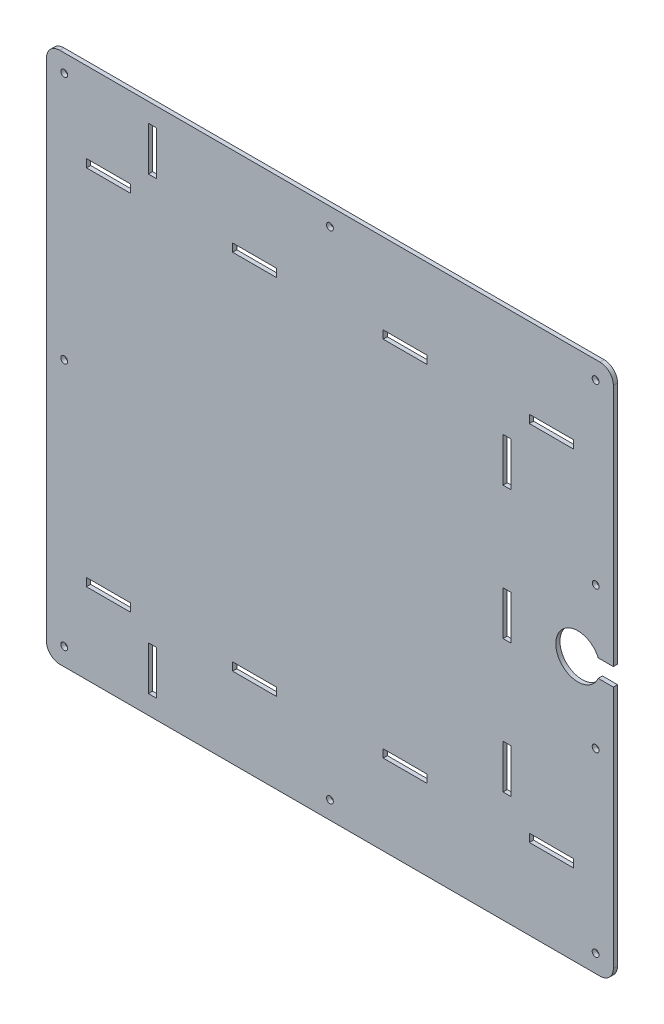
SolidWorks part; units mm, degrees
material "Balsa"
ref_plane "Front Plane" through (0, 0, 0) normal (0, 0, 1) x (1, 0, 0)
ref_plane "Top Plane" through (0, 0, 0) normal (0, 1, 0) x (1, 0, 0)
ref_plane "Right Plane" through (0, 0, 0) normal (1, 0, 0) x (0, 0, -1)
sketch "Sketch1" plane through (0, 0, 0) normal (0, 0, 1) x (1, 0, 0)
  line L0 (-135.8663, -66.675) -> (-135.8663, -314.579)
  line L39 (270.5337, -82.55) -> (270.5337, -9.525)
  line L40 (261.0087, 0) -> (-126.3413, 0)
  line L41 (-135.8663, -9.525) -> (-135.8663, -66.675)
  line L49 (259.6834, -184.277) -> (270.5337, -184.277)
  line L50 (270.5337, -184.277) -> (270.5337, -82.55)
  line L66 (270.5337, -298.704) -> (270.5337, -196.977)
  line L67 (270.5337, -196.977) -> (259.6834, -196.977)
  line L68 (270.5337, -371.729) -> (270.5337, -298.704)
  line L76 (-135.8663, -314.579) -> (-135.8663, -371.729)
  line L77 (-126.3413, -381.254) -> (261.0087, -381.254)
  arc A7 (270.5337, -9.525) -> (261.0087, 0) centre (261.0087, -9.525) ccw
  arc A8 (-126.3413, 0) -> (-135.8663, -9.525) centre (-126.3413, -9.525) ccw
  arc A10 (259.6834, -184.277) -> (259.6834, -196.977) centre (245.1337, -190.627) ccw
  arc A12 (-135.8663, -371.729) -> (-126.3413, -381.254) centre (-126.3413, -371.729) ccw
  arc A13 (261.0087, -381.254) -> (270.5337, -371.729) centre (261.0087, -371.729) ccw
  dimension "D4" = 15.875
  dimension "D5" = 9.525
  dimension "D1" = 406.4
  dimension "D2" = 381.254
  dimension "D3" = 25.4
  dimension "D6" = 245.1337
  dimension "D7" = 259.6834
  dimension "D8" = 66.675
  dimension "D9" = 82.55
  dimension "D10" = 12.7
extrude "Boss-Extrude1" add sketch "Sketch1" along normal blind 3
hole_wizard "#10 (0.1935) Diameter Hole3" positions "3DSketch1" profile "Sketch2" hole size "#10" standard "ANSI Inch"
sketch3d "3DSketch1"
  line L0 (261.0087, 0, 3) -> (-126.3413, 0, 3) construction
  line L1 (-135.8663, -9.525, 3) -> (-135.8663, -371.729, 3) construction
  point P0 (-123.1663, -12.7, 3)
  dimension "D1" = 12.7
  dimension "D2" = 12.7
sketch "Sketch2" plane through (-123.1663, -12.7, 3) normal (1, 0, 0) x (0, -1, 0)
  line L0 (0, 0) -> (0, 77.6766)
  line L1 (0, 77.6766) -> (2.4574, 76.2)
  line L2 (2.4574, 76.2) -> (2.4574, 0)
  line L5 (2.4574, 0) -> (0, 0)
  line L10 (0, 77.6766) -> (-2.4575, 76.2) construction
  line L11 (0, -6.35) -> (0, 107.95) construction
  dimension "Hole Dia." = 4.9149
  dimension "Hole Depth" = 76.2
  dimension "Drill Angle" = 118
ref_plane "Plane2" through (67.3337, 0, 0) normal (-1, 0, 0) x (0, 0, 1)
ref_plane "Plane3" through (0, -190.627, 0) normal (0, 1, 0) x (1, 0, 0)
hole_wizard "#10 (0.1935) Diameter Hole2" positions "3DSketch3" profile "Sketch7" hole size "#10" standard "ANSI Inch"
sketch3d "3DSketch3"
  line L0 (261.0087, 0, 0) -> (-126.3413, 0, 0) construction
  line L1 (67.3337, -381.254, 0) -> (67.3337, 0, 0) construction
  line L2 (-126.3413, -381.254, 0) -> (261.0087, -381.254, 0) construction
  line L4 (-135.8663, -190.627, 0) -> (306.0951, -190.627, 0) construction
  line L5 (-135.8663, -9.525, 0) -> (-135.8663, -371.729, 0) construction
  point P0 (67.3337, -12.7, 0)
  point P16 (-123.1663, -190.627, 0)
  dimension "D1" = 12.7
  dimension "D2" = 12.7
sketch "Sketch7" plane through (67.3337, -12.7, 0) normal (1, 0, 0) x (0, 1, 0)
  line L0 (0, 0) -> (0, 77.6766)
  line L1 (0, 77.6766) -> (2.4574, 76.2)
  line L2 (2.4574, 76.2) -> (2.4574, 0)
  line L5 (2.4574, 0) -> (0, 0)
  line L10 (0, 77.6766) -> (-2.4575, 76.2) construction
  line L11 (0, -6.35) -> (0, 107.95) construction
  dimension "Hole Dia." = 4.9149
  dimension "Hole Depth" = 76.2
  dimension "Drill Angle" = 118
mirror "Mirror1" about plane through (67.3337, 0, 0) normal (-1, 0, 0) of "#10 (0.1935) Diameter Hole3"
mirror "Mirror2" about plane through (0, -190.627, 0) normal (0, 1, 0) of "Mirror1", "#10 (0.1935) Diameter Hole3", "#10 (0.1935) Diameter Hole2"
hole_wizard "#10 (0.1935) Diameter Hole1" positions "3DSketch4" profile "Sketch8" hole size "#10" standard "ANSI Inch"
sketch3d "3DSketch4"
  line L0 (257.8337, -241.427, 0) -> (257.901, -139.827, 0) construction
  line L2 (-135.8663, -190.627, 0) -> (369.2975, -190.627, 0) construction
  line L3 (-135.8663, -9.525, 0) -> (-135.8663, -371.729, 0) construction
  line L5 (270.5337, -371.729, 0) -> (270.5337, -196.977, 0) construction
  point P0 (257.8337, -241.427, 0)
  point P2 (257.901, -139.827, 0)
  point P13 (257.8674, -190.627, 0)
  dimension "D1" = 12.7
  dimension "D2" = 101.6
sketch "Sketch8" plane through (257.8337, -241.427, 0) normal (1, 0, 0) x (0, 1, 0)
  line L0 (0, 0) -> (0, 77.6766)
  line L1 (0, 77.6766) -> (2.4574, 76.2)
  line L2 (2.4574, 76.2) -> (2.4574, 0)
  line L5 (2.4574, 0) -> (0, 0)
  line L10 (0, 77.6766) -> (-2.4575, 76.2) construction
  line L11 (0, -6.35) -> (0, 107.95) construction
  dimension "Hole Dia." = 4.9149
  dimension "Hole Depth" = 76.2
  dimension "Drill Angle" = 118
sketch "Sketch9" plane through (0, 0, 0) normal (0, 0, -1) x (-1, 0, 0)
  line L0 (-270.5337, -371.729) -> (-270.5337, -196.977) construction
  line L1 (-210.3103, -323.5579) -> (-241.8571, -323.5579)
  line L2 (-210.3103, -323.5579) -> (-210.3103, -317.7921)
  line L3 (-210.3103, -317.7921) -> (-241.8571, -317.7921)
  line L4 (-241.8571, -323.5579) -> (-241.8571, -317.7921)
  line L5 (-210.3103, -323.5579) -> (-241.8571, -317.7921) construction
  line L6 (-210.3103, -317.7921) -> (-241.8571, -323.5579) construction
  line L7 (-105.5353, -63.4619) -> (-137.0821, -57.6961) construction
  line L8 (-67.3337, -381.254) -> (-67.3337, 0) construction
  line L9 (126.3413, -381.254) -> (-261.0087, -381.254) construction
  line L10 (-261.0087, 0) -> (126.3413, 0) construction
  line L11 (135.8663, -190.627) -> (-400.4137, -190.627) construction
  line L12 (135.8663, -9.525) -> (135.8663, -371.729) construction
  line L13 (75.6429, -323.5579) -> (75.6429, -317.7921)
  line L14 (75.6429, -317.7921) -> (107.1897, -317.7921)
  line L15 (107.1897, -323.5579) -> (107.1897, -317.7921)
  line L16 (75.6429, -323.5579) -> (107.1897, -323.5579)
  line L19 (-241.8571, -57.6961) -> (-241.8571, -63.4619)
  line L25 (-191.4508, -79.6036) -> (-197.2166, -79.6036)
  line L26 (-191.4508, -301.6504) -> (-197.2166, -301.6504)
  line L27 (-191.4508, -301.6504) -> (-191.4508, -270.1036)
  line L28 (-191.4508, -270.1036) -> (-197.2166, -270.1036)
  line L29 (-197.2166, -301.6504) -> (-197.2166, -270.1036)
  line L30 (-191.4508, -301.6504) -> (-197.2166, -270.1036) construction
  line L31 (-191.4508, -270.1036) -> (-197.2166, -301.6504) construction
  line L32 (-197.2166, -79.6036) -> (-197.2166, -111.1504)
  line L33 (-191.4508, -111.1504) -> (-197.2166, -111.1504)
  line L34 (-191.4508, -79.6036) -> (-191.4508, -111.1504)
  line L35 (-29.1321, -323.5579) -> (-29.1321, -317.7921)
  line L36 (-197.2166, -206.4004) -> (-191.4508, -206.4004)
  line L37 (-197.2166, -206.4004) -> (-197.2166, -174.8536)
  line L38 (-197.2166, -174.8536) -> (-191.4508, -174.8536)
  line L39 (-191.4508, -206.4004) -> (-191.4508, -174.8536)
  line L40 (-197.2166, -206.4004) -> (-191.4508, -174.8536) construction
  line L41 (-197.2166, -174.8536) -> (-191.4508, -206.4004) construction
  line L42 (-105.5353, -323.5579) -> (-137.0821, -323.5579)
  line L43 (-105.5353, -323.5579) -> (-105.5353, -317.7921)
  line L44 (-105.5353, -317.7921) -> (-137.0821, -317.7921)
  line L45 (-137.0821, -323.5579) -> (-137.0821, -317.7921)
  line L46 (-105.5353, -323.5579) -> (-137.0821, -317.7921) construction
  line L47 (-105.5353, -317.7921) -> (-137.0821, -323.5579) construction
  line L48 (-29.1321, -317.7921) -> (2.4147, -317.7921)
  line L49 (2.4147, -323.5579) -> (2.4147, -317.7921)
  line L50 (-29.1321, -323.5579) -> (2.4147, -323.5579)
  line L51 (-105.5353, -57.6961) -> (-137.0821, -63.4619) construction
  line L52 (-210.3103, -63.4619) -> (-241.8571, -57.6961) construction
  line L53 (-210.3103, -57.6961) -> (-241.8571, -63.4619) construction
  line L54 (-29.1321, -57.6961) -> (2.4147, -57.6961)
  line L55 (2.4147, -57.6961) -> (2.4147, -63.4619)
  line L56 (-29.1321, -63.4619) -> (2.4147, -63.4619)
  line L57 (-137.0821, -57.6961) -> (-137.0821, -63.4619)
  line L58 (-105.5353, -63.4619) -> (-137.0821, -63.4619)
  line L59 (-105.5353, -57.6961) -> (-105.5353, -63.4619)
  line L60 (-105.5353, -57.6961) -> (-137.0821, -57.6961)
  line L61 (-29.1321, -57.6961) -> (-29.1321, -63.4619)
  line L62 (75.6429, -57.6961) -> (107.1897, -57.6961)
  line L63 (107.1897, -57.6961) -> (107.1897, -63.4619)
  line L64 (75.6429, -63.4619) -> (107.1897, -63.4619)
  line L65 (75.6429, -57.6961) -> (75.6429, -63.4619)
  line L66 (-241.8571, -57.6961) -> (-241.8571, -63.4619)
  line L67 (-210.3103, -63.4619) -> (-241.8571, -63.4619)
  line L68 (-210.3103, -57.6961) -> (-210.3103, -63.4619)
  line L69 (-210.3103, -57.6961) -> (-241.8571, -57.6961)
  line L70 (57.0501, -13.5712) -> (62.8159, -13.5712)
  line L71 (57.0501, -367.6828) -> (62.8159, -367.6828)
  line L72 (57.0501, -367.6828) -> (57.0501, -336.136)
  line L73 (57.0501, -336.136) -> (62.8159, -336.136)
  line L74 (62.8159, -367.6828) -> (62.8159, -336.136)
  line L75 (57.0501, -367.6828) -> (62.8159, -336.136) construction
  line L76 (57.0501, -336.136) -> (62.8159, -367.6828) construction
  line L77 (62.8159, -13.5712) -> (62.8159, -45.118)
  line L78 (57.0501, -45.118) -> (62.8159, -45.118)
  line L79 (57.0501, -13.5712) -> (57.0501, -45.118)
  line L80 (135.8663, -9.525) -> (135.8663, -371.729) construction
  point P0 (-226.0837, -320.675)
  point P25 (-241.8571, -60.579)
  point P30 (-194.3337, -285.877)
  point P39 (-194.3337, -190.627)
  point P44 (-121.3087, -320.675)
  point P53 (-13.3587, -323.5579)
  point P62 (-121.3087, -60.579)
  point P63 (-226.0837, -60.579)
  point P64 (59.933, -351.9094)
  dimension "D1" = 44.45
  dimension "D2" = 31.5468
  dimension "D3" = 5.7658
  dimension "D4" = 260.096
  dimension "D5" = 76.2
  dimension "D6" = 95.25
  dimension "D7" = 107.95
  dimension "D8" = 73.0504
  dimension "D9" = 28.3515
extrude "Cut-Extrude1" cut sketch "Sketch9" against normal through all contours L45 L42 L43 L44 | L4 L1 L2 L3 | L29 L26 L27 L28 | L36 L39 L38 L37 | L34 L25 L32 L33 | L68 L69 L19 L67 | L59 L60 L57 L58 | L54 L61 L56 L55 | L62 L65 L64 L63 | L71 L74 L73 L72 | L70 L79 L78 L77 | L14 L15 L16 L13 | L48 L49 L50 L35
sketch "Sketch10" plane through (0, 0, 3) normal (0, 0, 1) x (1, 0, 0)
  line L0 (-62.7143, -13.6728) -> (-62.7143, -45.0164)
  line L1 (-62.7143, -45.0164) -> (-57.1517, -45.0164)
  line L2 (-57.1517, -45.0164) -> (-57.1517, -13.6728)
  line L3 (-57.1517, -13.6728) -> (-62.7143, -13.6728)
  line L4 (-62.8159, -13.5712) -> (-62.8159, -45.118)
  line L5 (-57.0501, -13.5712) -> (-62.8159, -13.5712)
  line L6 (-57.0501, -45.118) -> (-57.0501, -13.5712)
  line L7 (270.5337, -184.277) -> (270.5337, -9.525)
  line L8 (261.0087, 0) -> (-126.3413, 0)
  line L9 (-135.8663, -9.525) -> (-135.8663, -371.729)
  line L10 (-126.3413, -381.254) -> (261.0087, -381.254)
  line L11 (270.5337, -371.729) -> (270.5337, -196.977)
  line L12 (270.5337, -196.977) -> (259.6834, -196.977)
  line L13 (259.6834, -184.277) -> (270.5337, -184.277)
  line L14 (270.5337, -184.277) -> (270.5337, -9.525) construction
  line L15 (261.0087, 0) -> (-126.3413, 0) construction
  line L16 (-135.8663, -9.525) -> (-135.8663, -371.729) construction
  line L17 (-126.3413, -381.254) -> (261.0087, -381.254) construction
  line L18 (270.5337, -371.729) -> (270.5337, -196.977) construction
  line L19 (270.5337, -196.977) -> (259.6834, -196.977) construction
  line L20 (259.6834, -184.277) -> (270.5337, -184.277) construction
  line L21 (-62.8159, -45.118) -> (-57.0501, -45.118)
  line L22 (-62.8159, -13.5712) -> (-62.8159, -45.118) construction
  line L23 (-57.0501, -13.5712) -> (-62.8159, -13.5712) construction
  line L24 (-57.0501, -45.118) -> (-57.0501, -13.5712) construction
  line L25 (-62.8159, -45.118) -> (-57.0501, -45.118) construction
  line L26 (-107.1897, -57.6961) -> (-107.1897, -63.4619)
  line L27 (-75.6429, -57.6961) -> (-107.1897, -57.6961)
  line L28 (-75.6429, -63.4619) -> (-75.6429, -57.6961)
  line L29 (-107.1897, -63.4619) -> (-75.6429, -63.4619)
  line L30 (-107.1897, -57.6961) -> (-107.1897, -63.4619) construction
  line L31 (-75.6429, -57.6961) -> (-107.1897, -57.6961) construction
  line L32 (-75.6429, -63.4619) -> (-75.6429, -57.6961) construction
  line L33 (-107.1897, -63.4619) -> (-75.6429, -63.4619) construction
  line L34 (-2.4147, -57.6961) -> (-2.4147, -63.4619)
  line L35 (29.1321, -57.6961) -> (-2.4147, -57.6961)
  line L36 (29.1321, -63.4619) -> (29.1321, -57.6961)
  line L37 (-2.4147, -63.4619) -> (29.1321, -63.4619)
  line L38 (-2.4147, -57.6961) -> (-2.4147, -63.4619) construction
  line L39 (29.1321, -57.6961) -> (-2.4147, -57.6961) construction
  line L40 (29.1321, -63.4619) -> (29.1321, -57.6961) construction
  line L41 (-2.4147, -63.4619) -> (29.1321, -63.4619) construction
  line L42 (105.5353, -63.4619) -> (137.0821, -63.4619)
  line L43 (105.5353, -57.6961) -> (105.5353, -63.4619)
  line L44 (137.0821, -57.6961) -> (105.5353, -57.6961)
  line L45 (137.0821, -63.4619) -> (137.0821, -57.6961)
  line L46 (105.5353, -63.4619) -> (137.0821, -63.4619) construction
  line L47 (105.5353, -57.6961) -> (105.5353, -63.4619) construction
  line L48 (137.0821, -57.6961) -> (105.5353, -57.6961) construction
  line L49 (137.0821, -63.4619) -> (137.0821, -57.6961) construction
  line L50 (210.3103, -63.4619) -> (241.8571, -63.4619)
  line L51 (210.3103, -57.6961) -> (210.3103, -63.4619)
  line L52 (241.8571, -57.6961) -> (210.3103, -57.6961)
  line L53 (241.8571, -63.4619) -> (241.8571, -57.6961)
  line L54 (210.3103, -63.4619) -> (241.8571, -63.4619) construction
  line L55 (210.3103, -57.6961) -> (210.3103, -63.4619) construction
  line L56 (241.8571, -57.6961) -> (210.3103, -57.6961) construction
  line L57 (241.8571, -63.4619) -> (241.8571, -57.6961) construction
  line L58 (191.4508, -111.1504) -> (197.2166, -111.1504)
  line L59 (191.4508, -79.6036) -> (191.4508, -111.1504)
  line L60 (197.2166, -79.6036) -> (191.4508, -79.6036)
  line L61 (197.2166, -111.1504) -> (197.2166, -79.6036)
  line L62 (191.4508, -111.1504) -> (197.2166, -111.1504) construction
  line L63 (191.4508, -79.6036) -> (191.4508, -111.1504) construction
  line L64 (197.2166, -79.6036) -> (191.4508, -79.6036) construction
  line L65 (197.2166, -111.1504) -> (197.2166, -79.6036) construction
  line L66 (191.4508, -206.4004) -> (197.2166, -206.4004)
  line L67 (191.4508, -174.8536) -> (191.4508, -206.4004)
  line L68 (197.2166, -174.8536) -> (191.4508, -174.8536)
  line L69 (197.2166, -206.4004) -> (197.2166, -174.8536)
  line L70 (191.4508, -206.4004) -> (197.2166, -206.4004) construction
  line L71 (191.4508, -174.8536) -> (191.4508, -206.4004) construction
  line L72 (197.2166, -174.8536) -> (191.4508, -174.8536) construction
  line L73 (197.2166, -206.4004) -> (197.2166, -174.8536) construction
  line L74 (197.2166, -270.1036) -> (191.4508, -270.1036)
  line L75 (197.2166, -301.6504) -> (197.2166, -270.1036)
  line L76 (191.4508, -301.6504) -> (197.2166, -301.6504)
  line L77 (191.4508, -270.1036) -> (191.4508, -301.6504)
  line L78 (197.2166, -270.1036) -> (191.4508, -270.1036) construction
  line L79 (197.2166, -301.6504) -> (197.2166, -270.1036) construction
  line L80 (191.4508, -301.6504) -> (197.2166, -301.6504) construction
  line L81 (191.4508, -270.1036) -> (191.4508, -301.6504) construction
  line L82 (241.8571, -317.7921) -> (210.3103, -317.7921)
  line L83 (241.8571, -323.5579) -> (241.8571, -317.7921)
  line L84 (210.3103, -323.5579) -> (241.8571, -323.5579)
  line L85 (210.3103, -317.7921) -> (210.3103, -323.5579)
  line L86 (241.8571, -317.7921) -> (210.3103, -317.7921) construction
  line L87 (241.8571, -323.5579) -> (241.8571, -317.7921) construction
  line L88 (210.3103, -323.5579) -> (241.8571, -323.5579) construction
  line L89 (210.3103, -317.7921) -> (210.3103, -323.5579) construction
  line L90 (137.0821, -317.7921) -> (105.5353, -317.7921)
  line L91 (137.0821, -323.5579) -> (137.0821, -317.7921)
  line L92 (105.5353, -323.5579) -> (137.0821, -323.5579)
  line L93 (105.5353, -317.7921) -> (105.5353, -323.5579)
  line L94 (137.0821, -317.7921) -> (105.5353, -317.7921) construction
  line L95 (137.0821, -323.5579) -> (137.0821, -317.7921) construction
  line L96 (105.5353, -323.5579) -> (137.0821, -323.5579) construction
  line L97 (105.5353, -317.7921) -> (105.5353, -323.5579) construction
  line L98 (29.1321, -317.7921) -> (-2.4147, -317.7921)
  line L99 (29.1321, -323.5579) -> (29.1321, -317.7921)
  line L100 (-2.4147, -323.5579) -> (29.1321, -323.5579)
  line L101 (-2.4147, -317.7921) -> (-2.4147, -323.5579)
  line L102 (29.1321, -317.7921) -> (-2.4147, -317.7921) construction
  line L103 (29.1321, -323.5579) -> (29.1321, -317.7921) construction
  line L104 (-2.4147, -323.5579) -> (29.1321, -323.5579) construction
  line L105 (-2.4147, -317.7921) -> (-2.4147, -323.5579) construction
  line L106 (-62.8159, -367.6828) -> (-57.0501, -367.6828)
  line L107 (-62.8159, -336.136) -> (-62.8159, -367.6828)
  line L108 (-57.0501, -336.136) -> (-62.8159, -336.136)
  line L109 (-57.0501, -367.6828) -> (-57.0501, -336.136)
  line L110 (-62.8159, -367.6828) -> (-57.0501, -367.6828) construction
  line L111 (-62.8159, -336.136) -> (-62.8159, -367.6828) construction
  line L112 (-57.0501, -336.136) -> (-62.8159, -336.136) construction
  line L113 (-57.0501, -367.6828) -> (-57.0501, -336.136) construction
  line L114 (-75.6429, -317.7921) -> (-107.1897, -317.7921)
  line L115 (-75.6429, -323.5579) -> (-75.6429, -317.7921)
  line L116 (-107.1897, -323.5579) -> (-75.6429, -323.5579)
  line L117 (-107.1897, -317.7921) -> (-107.1897, -323.5579)
  line L118 (-75.6429, -317.7921) -> (-107.1897, -317.7921) construction
  line L119 (-75.6429, -323.5579) -> (-75.6429, -317.7921) construction
  line L120 (-107.1897, -323.5579) -> (-75.6429, -323.5579) construction
  line L121 (-107.1897, -317.7921) -> (-107.1897, -323.5579) construction
  line L122 (-107.0881, -57.7977) -> (-107.0881, -63.3603)
  line L123 (-107.0881, -63.3603) -> (-75.7445, -63.3603)
  line L124 (-75.7445, -63.3603) -> (-75.7445, -57.7977)
  line L125 (-75.7445, -57.7977) -> (-107.0881, -57.7977)
  line L126 (197.115, -301.5488) -> (197.115, -270.2052)
  line L127 (197.115, -270.2052) -> (191.5524, -270.2052)
  line L128 (191.5524, -270.2052) -> (191.5524, -301.5488)
  line L129 (191.5524, -301.5488) -> (197.115, -301.5488)
  line L130 (241.7555, -317.8937) -> (210.4119, -317.8937)
  line L131 (210.4119, -317.8937) -> (210.4119, -323.4563)
  line L132 (210.4119, -323.4563) -> (241.7555, -323.4563)
  line L133 (241.7555, -323.4563) -> (241.7555, -317.8937)
  line L134 (136.9805, -317.8937) -> (105.6369, -317.8937)
  line L135 (105.6369, -317.8937) -> (105.6369, -323.4563)
  line L136 (105.6369, -323.4563) -> (136.9805, -323.4563)
  line L137 (136.9805, -323.4563) -> (136.9805, -317.8937)
  line L138 (29.0305, -317.8937) -> (-2.3131, -317.8937)
  line L139 (-2.3131, -317.8937) -> (-2.3131, -323.4563)
  line L140 (-2.3131, -323.4563) -> (29.0305, -323.4563)
  line L141 (29.0305, -323.4563) -> (29.0305, -317.8937)
  line L142 (-62.7143, -367.5812) -> (-57.1517, -367.5812)
  line L143 (-57.1517, -367.5812) -> (-57.1517, -336.2376)
  line L144 (-57.1517, -336.2376) -> (-62.7143, -336.2376)
  line L145 (-62.7143, -336.2376) -> (-62.7143, -367.5812)
  line L146 (-75.7445, -317.8937) -> (-107.0881, -317.8937)
  line L147 (-107.0881, -317.8937) -> (-107.0881, -323.4563)
  line L148 (-107.0881, -323.4563) -> (-75.7445, -323.4563)
  line L149 (-75.7445, -323.4563) -> (-75.7445, -317.8937)
  line L150 (-2.3131, -57.7977) -> (-2.3131, -63.3603)
  line L151 (-2.3131, -63.3603) -> (29.0305, -63.3603)
  line L152 (29.0305, -63.3603) -> (29.0305, -57.7977)
  line L153 (29.0305, -57.7977) -> (-2.3131, -57.7977)
  line L154 (105.6369, -63.3603) -> (136.9805, -63.3603)
  line L155 (136.9805, -63.3603) -> (136.9805, -57.7977)
  line L156 (136.9805, -57.7977) -> (105.6369, -57.7977)
  line L157 (105.6369, -57.7977) -> (105.6369, -63.3603)
  line L158 (191.5524, -111.0488) -> (197.115, -111.0488)
  line L159 (197.115, -111.0488) -> (197.115, -79.7052)
  line L160 (197.115, -79.7052) -> (191.5524, -79.7052)
  line L161 (191.5524, -79.7052) -> (191.5524, -111.0488)
  line L162 (191.5524, -206.2988) -> (197.115, -206.2988)
  line L163 (197.115, -206.2988) -> (197.115, -174.9552)
  line L164 (197.115, -174.9552) -> (191.5524, -174.9552)
  line L165 (191.5524, -174.9552) -> (191.5524, -206.2988)
  line L166 (210.4119, -63.3603) -> (241.7555, -63.3603)
  line L167 (241.7555, -63.3603) -> (241.7555, -57.7977)
  line L168 (241.7555, -57.7977) -> (210.4119, -57.7977)
  line L169 (210.4119, -57.7977) -> (210.4119, -63.3603)
  line L170 (-126.3413, -381.3556) -> (261.0087, -381.3556)
  line L171 (270.6353, -371.729) -> (270.6353, -196.8754)
  line L172 (270.6353, -196.8754) -> (259.6168, -196.8754)
  line L173 (259.6168, -184.3786) -> (270.6353, -184.3786)
  line L174 (270.6353, -184.3786) -> (270.6353, -9.525)
  line L175 (261.0087, 0.1016) -> (-126.3413, 0.1016)
  line L176 (-135.9679, -9.525) -> (-135.9679, -371.729)
  circle A0 centre (257.8337, -368.554) radius 2.3558
  circle A1 centre (67.3337, -12.7) radius 2.4574
  circle A2 centre (67.3337, -12.7) radius 2.4574 construction
  circle A3 centre (-123.1663, -12.7) radius 2.4574
  circle A4 centre (-123.1663, -12.7) radius 2.4574 construction
  arc A5 (270.5337, -9.525) -> (261.0087, 0) centre (261.0087, -9.525) ccw
  arc A6 (-126.3413, 0) -> (-135.8663, -9.525) centre (-126.3413, -9.525) ccw
  arc A7 (-135.8663, -371.729) -> (-126.3413, -381.254) centre (-126.3413, -371.729) ccw
  arc A8 (261.0087, -381.254) -> (270.5337, -371.729) centre (261.0087, -371.729) ccw
  arc A9 (259.6834, -184.277) -> (259.6834, -196.977) centre (245.1337, -190.627) ccw
  arc A10 (270.5337, -9.525) -> (261.0087, 0) centre (261.0087, -9.525) ccw construction
  arc A11 (-126.3413, 0) -> (-135.8663, -9.525) centre (-126.3413, -9.525) ccw construction
  arc A12 (-135.8663, -371.729) -> (-126.3413, -381.254) centre (-126.3413, -371.729) ccw construction
  arc A13 (261.0087, -381.254) -> (270.5337, -371.729) centre (261.0087, -371.729) ccw construction
  arc A14 (259.6834, -184.277) -> (259.6834, -196.977) centre (245.1337, -190.627) ccw construction
  circle A15 centre (257.8337, -12.7) radius 2.4574
  circle A16 centre (257.8337, -12.7) radius 2.4574 construction
  circle A17 centre (257.901, -139.827) radius 2.4574
  circle A18 centre (257.901, -139.827) radius 2.4574 construction
  circle A19 centre (257.8337, -241.427) radius 2.4574
  circle A20 centre (257.8337, -241.427) radius 2.4574 construction
  circle A21 centre (257.8337, -368.554) radius 2.4574
  circle A22 centre (257.8337, -368.554) radius 2.4574 construction
  circle A23 centre (67.3337, -368.554) radius 2.4574
  circle A24 centre (67.3337, -368.554) radius 2.4574 construction
  circle A25 centre (-123.1663, -190.627) radius 2.4574
  circle A26 centre (-123.1663, -190.627) radius 2.4574 construction
  circle A27 centre (-123.1663, -368.554) radius 2.4574
  circle A28 centre (-123.1663, -368.554) radius 2.4574 construction
  circle A29 centre (67.3337, -368.554) radius 2.3558
  circle A30 centre (257.8337, -241.427) radius 2.3559
  circle A31 centre (257.8337, -12.7) radius 2.3559
  circle A32 centre (257.901, -139.827) radius 2.3559
  circle A33 centre (-123.1663, -12.7) radius 2.3558
  circle A34 centre (-123.1663, -190.627) radius 2.3558
  circle A35 centre (-123.1663, -368.554) radius 2.3558
  circle A36 centre (67.3337, -12.7) radius 2.3558
  arc A37 (261.0087, -381.3556) -> (270.6353, -371.729) centre (261.0087, -371.729) ccw
  arc A38 (259.6168, -184.3786) -> (259.6168, -196.8754) centre (245.1337, -190.627) ccw
  arc A39 (270.6353, -9.525) -> (261.0087, 0.1016) centre (261.0087, -9.525) ccw
  arc A40 (-126.3413, 0.1016) -> (-135.9679, -9.525) centre (-126.3413, -9.525) ccw
  arc A41 (-135.9679, -371.729) -> (-126.3413, -381.3556) centre (-126.3413, -371.729) ccw
  dimension "D1" = 0
  dimension "D2" = 0
  dimension "D3" = 0
  dimension "D4" = 0
  dimension "D5" = 0
  dimension "D6" = 0
  dimension "D7" = 0
  dimension "D8" = 0
  dimension "D9" = 0
  dimension "D10" = 0
  dimension "D11" = 0
  dimension "D12" = 0
  dimension "D13" = 0
  dimension "D14" = 0
  dimension "D15" = 0
  dimension "D16" = 0
  dimension "D17" = 0
  dimension "D18" = 0
  dimension "D19" = 0
  dimension "D20" = 0
  dimension "D21" = 0
  dimension "D22" = 0
  dimension "D23" = 0
  dimension "D24" = 0.1016
  dimension "D25" = 0.1016
extrude "KERF" [suppressed] add sketch "Sketch10" along normal blind 3.175 separate body
